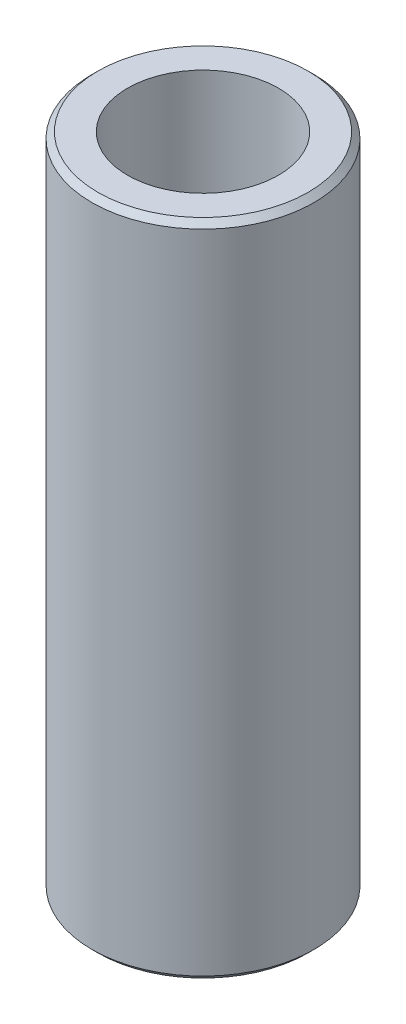
SolidWorks part; units mm, degrees
material "6061-T6 (SS)"
ref_plane "Front Plane" through (0, 0, 0) normal (0, 0, 1) x (1, 0, 0)
ref_plane "Top Plane" through (0, 0, 0) normal (0, 1, 0) x (1, 0, 0)
ref_plane "Right Plane" through (0, 0, 0) normal (1, 0, 0) x (0, 0, -1)
sketch "Sketch1" plane through (0, 0, 0) normal (0, 1, 0) x (1, 0, 0)
  circle A0 centre (0, 0) radius 4.7625
  dimension "D1" = 9.525
extrude "Boss-Extrude1" add sketch "Sketch1" along normal mid plane 28.2575
chamfer "Chamfer1" distance 0.254 angle 45 2 edges at (0, 14.1288, 4.7625) (0, -14.1288, 4.7625)
sketch "Sketch2" plane through (0, -14.1288, 0) normal (0, -1, 0) x (1, 0, 0)
  circle A0 centre (0, 0) radius 3.2385
  dimension "D1" = 6.477
extrude "Cut-Extrude1" cut sketch "Sketch2" against normal through all
